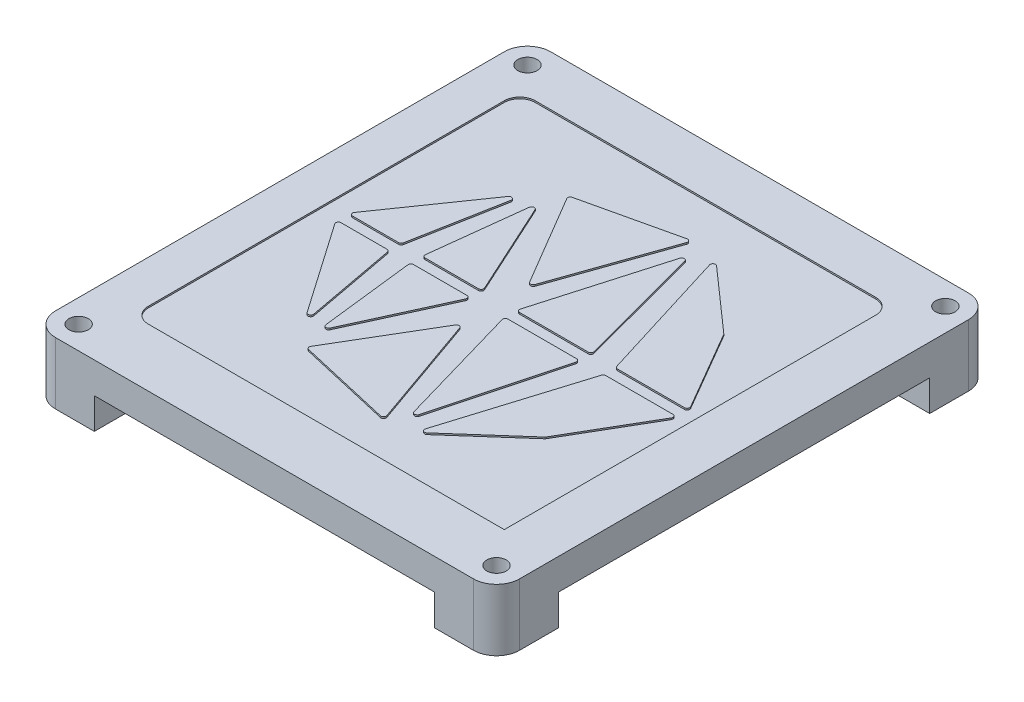
SolidWorks part; units mm, degrees
ref_plane "前视基准面" through (0, 0, 0) normal (0, 0, 1) x (1, 0, 0)
ref_plane "上视基准面" through (0, 0, 0) normal (0, 1, 0) x (1, 0, 0)
ref_plane "右视基准面" through (0, 0, 0) normal (1, 0, 0) x (0, 0, -1)
other "Configuration Table"
sketch "草图1" plane through (0, 0, 0) normal (0, 1, 0) x (1, 0, 0)
  line L8 (-27.0001, -31.9874) -> (27.0001, -31.9874)
  line L9 (29.9874, -29.0001) -> (29.9874, 29.0001)
  line L10 (27.0001, 31.9874) -> (-27.0001, 31.9874)
  line L11 (-29.9874, 29.0001) -> (-29.9874, -29.0001)
  line L12 (-27.0001, -31.9874) -> (27.0001, -31.9874)
  line L13 (29.9874, -29.0001) -> (29.9874, 29.0001)
  line L14 (27.0001, 31.9874) -> (-27.0001, 31.9874)
  line L15 (-29.9874, 29.0001) -> (-29.9874, -29.0001)
  arc A4 (27.0001, -31.9874) -> (29.9874, -29.0001) centre (27.0001, -29.0001) ccw
  arc A5 (29.9874, 29.0001) -> (27.0001, 31.9874) centre (27.0001, 29.0001) ccw
  arc A6 (-27.0001, 31.9874) -> (-29.9874, 29.0001) centre (-27.0001, 29.0001) ccw
  arc A7 (-29.9874, -29.0001) -> (-27.0001, -31.9874) centre (-27.0001, -29.0001) ccw
  arc A8 (27.0001, -31.9874) -> (29.9874, -29.0001) centre (27.0001, -29.0001) ccw
  arc A9 (29.9874, 29.0001) -> (27.0001, 31.9874) centre (27.0001, 29.0001) ccw
  arc A10 (-27.0001, 31.9874) -> (-29.9874, 29.0001) centre (-27.0001, 29.0001) ccw
  arc A11 (-29.9874, -29.0001) -> (-27.0001, -31.9874) centre (-27.0001, -29.0001) ccw
  dimension "D1" = 0
extrude "凸台-拉伸1" add sketch "草图1" along normal blind 4
sketch "草图2" plane through (0, 0, 0) normal (0, -1, 0) x (1, 0, 0)
  line L4 (-21.9874, 23.9874) -> (-21.9874, 31.9874)
  line L5 (-21.9874, 31.9874) -> (-27.0001, 31.9874)
  line L6 (-29.9874, 29.0001) -> (-29.9874, 23.9874)
  line L7 (-29.9874, 23.9874) -> (-21.9874, 23.9874)
  line L8 (-21.9874, 23.9874) -> (-21.9874, 31.9874)
  line L9 (-21.9874, 31.9874) -> (-27.0001, 31.9874)
  line L10 (-29.9874, 29.0001) -> (-29.9874, 23.9874)
  line L11 (-29.9874, 23.9874) -> (-21.9874, 23.9874)
  line L12 (21.9874, -23.9874) -> (21.9874, -31.9874)
  line L13 (21.9874, -31.9874) -> (27.0001, -31.9874)
  line L14 (29.9874, -29.0001) -> (29.9874, -23.9874)
  line L15 (29.9874, -23.9874) -> (21.9874, -23.9874)
  line L16 (21.9874, -23.9874) -> (21.9874, -31.9874)
  line L17 (21.9874, -31.9874) -> (27.0001, -31.9874)
  line L18 (29.9874, -29.0001) -> (29.9874, -23.9874)
  line L19 (29.9874, -23.9874) -> (21.9874, -23.9874)
  line L20 (21.9874, 23.9874) -> (29.9874, 23.9874)
  line L21 (29.9874, 23.9874) -> (29.9874, 29.0001)
  line L22 (27.0001, 31.9874) -> (21.9874, 31.9874)
  line L23 (21.9874, 31.9874) -> (21.9874, 23.9874)
  line L24 (21.9874, 23.9874) -> (29.9874, 23.9874)
  line L25 (29.9874, 23.9874) -> (29.9874, 29.0001)
  line L26 (27.0001, 31.9874) -> (21.9874, 31.9874)
  line L27 (21.9874, 31.9874) -> (21.9874, 23.9874)
  line L28 (-29.9874, -23.9874) -> (-29.9874, -29.0001)
  line L29 (-21.9874, -23.9874) -> (-29.9874, -23.9874)
  line L30 (-21.9874, -31.9874) -> (-21.9874, -23.9874)
  line L31 (-27.0001, -31.9874) -> (-21.9874, -31.9874)
  line L32 (-29.9874, -23.9874) -> (-29.9874, -29.0001)
  line L33 (-21.9874, -23.9874) -> (-29.9874, -23.9874)
  line L34 (-21.9874, -31.9874) -> (-21.9874, -23.9874)
  line L35 (-27.0001, -31.9874) -> (-21.9874, -31.9874)
  arc A1 (-27.0001, 31.9874) -> (-29.9874, 29.0001) centre (-27.0001, 29.0001) ccw
  arc A2 (-27.0001, 31.9874) -> (-29.9874, 29.0001) centre (-27.0001, 29.0001) ccw
  arc A3 (27.0001, -31.9874) -> (29.9874, -29.0001) centre (27.0001, -29.0001) ccw
  arc A4 (27.0001, -31.9874) -> (29.9874, -29.0001) centre (27.0001, -29.0001) ccw
  arc A5 (29.9874, 29.0001) -> (27.0001, 31.9874) centre (27.0001, 29.0001) ccw
  arc A6 (29.9874, 29.0001) -> (27.0001, 31.9874) centre (27.0001, 29.0001) ccw
  arc A7 (-29.9874, -29.0001) -> (-27.0001, -31.9874) centre (-27.0001, -29.0001) ccw
  arc A8 (-29.9874, -29.0001) -> (-27.0001, -31.9874) centre (-27.0001, -29.0001) ccw
  dimension "D1" = 0
  dimension "D2" = 0
  dimension "D3" = 0
  dimension "D4" = 0
extrude "凸台-拉伸2" add sketch "草图2" along normal blind 4
sketch "草图3" plane through (0, -4, 0) normal (0, -1, 0) x (1, 0, 0)
  circle A0 centre (-27.0001, 29.0001) radius 1.25
  circle A1 centre (27.0001, 29.0001) radius 1.25
  circle A2 centre (27.0001, -29.0001) radius 1.25
  circle A3 centre (-27.0001, -29.0001) radius 1.25
  dimension "D1" = 2.5
  dimension "D2" = 2.5
  dimension "D3" = 2.5
  dimension "D4" = 2.5
extrude "切除-拉伸1" cut sketch "草图3" against normal blind 15
sketch "草图5" plane through (0, 4, 0) normal (0, 1, 0) x (1, 0, 0)
  line L62 (-15.4572, -0.6885) -> (-21.4047, -0.6885)
  line L63 (-21.6811, -1.2171) -> (-13.5463, -12.9327)
  line L64 (-12.9389, -12.679) -> (-15.1263, -0.9633)
  line L65 (-13.5463, 13.0483) -> (-21.6811, 1.3327)
  line L66 (-21.4047, 0.8041) -> (-15.4572, 0.8041)
  line L67 (-15.1263, 1.0789) -> (-12.9389, 12.7946)
  line L68 (-10.9698, 13.2091) -> (-12.3754, 1.1798)
  line L69 (-12.0411, 0.8041) -> (-5.1311, 0.8041)
  line L70 (-4.825, 1.2808) -> (-10.3294, 13.3101)
  line L71 (-5.1311, -0.6885) -> (-12.0411, -0.6885)
  line L72 (-12.3754, -1.0642) -> (-10.9698, -13.0935)
  line L73 (-10.3294, -13.1945) -> (-4.825, -1.1652)
  line L74 (-2.5713, -4.7347) -> (-9.5126, -16.4728)
  line L75 (-9.2984, -16.9722) -> (2.7471, -19.7455)
  line L76 (3.1402, -19.3058) -> (-1.964, -4.7943)
  line L77 (5.1091, -17.1135) -> (9.3621, -1.1116)
  line L78 (9.0368, -0.6885) -> (0.1709, -0.6885)
  line L79 (-0.1525, -1.1183) -> (4.4604, -17.1202)
  line L80 (21.4842, -0.6885) -> (12.8085, -0.6885)
  line L81 (12.4869, -0.9258) -> (7.1237, -18.2969)
  line L82 (7.6683, -18.6483) -> (15.7557, -11.4981)
  line L83 (15.8237, -11.4153) -> (21.7751, -1.1945)
  line L84 (12.8085, 0.8041) -> (21.4842, 0.8041)
  line L85 (21.7751, 1.3101) -> (15.8237, 11.5309)
  line L86 (15.7557, 11.6137) -> (7.6683, 18.7639)
  line L87 (7.1237, 18.4125) -> (12.4869, 1.0414)
  line L88 (0.1709, 0.8041) -> (9.0368, 0.8041)
  line L89 (9.3621, 1.2272) -> (5.1091, 17.2291)
  line L90 (4.4604, 17.2358) -> (-0.1525, 1.2339)
  line L91 (-9.5126, 16.5885) -> (-2.5713, 4.8503)
  line L92 (-1.964, 4.91) -> (3.1402, 19.4214)
  line L93 (2.7471, 19.8611) -> (-9.2984, 17.0878)
  line L95 (-22.5102, -24.4894) -> (23.4898, -24.4894)
  line L96 (-24.5102, -22.4894) -> (-24.5102, 23.5106)
  line L97 (-22.5102, 25.5106) -> (21.4898, 25.5106)
  line L98 (23.4898, -24.4894) -> (23.4898, 23.5106)
  line L99 (-0.5102, 25.5106) -> (0.4898, -24.4894) construction
  line L100 (-24.5102, 0.5106) -> (23.4898, -0.4894) construction
  arc A48 (-15.1263, -0.9633) -> (-15.4572, -0.6885) centre (-15.4572, -1.0251) ccw
  arc A49 (-21.4047, -0.6885) -> (-21.6811, -1.2171) centre (-21.4047, -1.0251) ccw
  arc A50 (-13.5463, -12.9327) -> (-13.2698, -13.0773) centre (-13.2698, -12.7407) ccw
  arc A51 (-13.2698, -13.0773) -> (-12.9389, -12.679) centre (-13.2698, -12.7407) ccw
  arc A52 (-12.9389, 12.7946) -> (-13.5463, 13.0483) centre (-13.2698, 12.8564) ccw
  arc A53 (-21.6811, 1.3327) -> (-21.4047, 0.8041) centre (-21.4047, 1.1407) ccw
  arc A54 (-15.4572, 0.8041) -> (-15.1263, 1.0789) centre (-15.4572, 1.1407) ccw
  arc A55 (-10.3294, 13.3101) -> (-10.9698, 13.2091) centre (-10.6355, 13.1701) ccw
  arc A56 (-12.3754, 1.1798) -> (-12.0411, 0.8041) centre (-12.0411, 1.1407) ccw
  arc A57 (-5.1311, 0.8041) -> (-4.825, 1.2808) centre (-5.1311, 1.1407) ccw
  arc A58 (-4.825, -1.1652) -> (-5.1311, -0.6885) centre (-5.1311, -1.0251) ccw
  arc A59 (-12.0411, -0.6885) -> (-12.3754, -1.0642) centre (-12.0411, -1.0251) ccw
  arc A60 (-10.9698, -13.0935) -> (-10.6355, -13.391) centre (-10.6355, -13.0544) ccw
  arc A61 (-10.6355, -13.391) -> (-10.3294, -13.1945) centre (-10.6355, -13.0544) ccw
  arc A62 (-1.964, -4.7943) -> (-2.5713, -4.7347) centre (-2.2815, -4.906) ccw
  arc A63 (-9.5126, -16.4728) -> (-9.2984, -16.9722) centre (-9.2229, -16.6442) ccw
  arc A64 (2.7471, -19.7455) -> (2.8226, -19.7541) centre (2.8226, -19.4175) ccw
  arc A65 (2.8226, -19.7541) -> (3.1402, -19.3058) centre (2.8226, -19.4175) ccw
  arc A66 (4.4604, -17.1202) -> (4.7838, -17.3636) centre (4.7838, -17.027) ccw
  arc A67 (4.7838, -17.3636) -> (5.1091, -17.1135) centre (4.7838, -17.027) ccw
  arc A68 (9.3621, -1.1116) -> (9.0368, -0.6885) centre (9.0368, -1.0251) ccw
  arc A69 (0.1709, -0.6885) -> (-0.1525, -1.1183) centre (0.1709, -1.0251) ccw
  arc A70 (21.7751, -1.1945) -> (21.4842, -0.6885) centre (21.4842, -1.0251) ccw
  arc A71 (12.8085, -0.6885) -> (12.4869, -0.9258) centre (12.8085, -1.0251) ccw
  arc A72 (7.1237, -18.2969) -> (7.4453, -18.7328) centre (7.4453, -18.3962) ccw
  arc A73 (7.4453, -18.7328) -> (7.6683, -18.6483) centre (7.4453, -18.3962) ccw
  arc A74 (15.7557, -11.4981) -> (15.8237, -11.4153) centre (15.5328, -11.2459) ccw
  arc A75 (12.4869, 1.0414) -> (12.8085, 0.8041) centre (12.8085, 1.1407) ccw
  arc A76 (21.4842, 0.8041) -> (21.7751, 1.3101) centre (21.4842, 1.1407) ccw
  arc A77 (15.8237, 11.5309) -> (15.7557, 11.6137) centre (15.5328, 11.3615) ccw
  arc A78 (7.6683, 18.7639) -> (7.1237, 18.4125) centre (7.4453, 18.5118) ccw
  arc A79 (-0.1525, 1.2339) -> (0.1709, 0.8041) centre (0.1709, 1.1407) ccw
  arc A80 (9.0368, 0.8041) -> (9.3621, 1.2272) centre (9.0368, 1.1407) ccw
  arc A81 (5.1091, 17.2291) -> (4.4604, 17.2358) centre (4.7838, 17.1426) ccw
  arc A82 (-9.2984, 17.0878) -> (-9.5126, 16.5885) centre (-9.2229, 16.7598) ccw
  arc A83 (-2.5713, 4.8503) -> (-2.2815, 4.685) centre (-2.2815, 5.0216) ccw
  arc A84 (-2.2815, 4.685) -> (-1.964, 4.91) centre (-2.2815, 5.0216) ccw
  arc A85 (3.1402, 19.4214) -> (2.7471, 19.8611) centre (2.8226, 19.5331) ccw
  arc A86 (-24.5102, 23.5106) -> (-22.5102, 25.5106) centre (-22.5102, 23.5106) cw
  arc A87 (-22.5102, -24.4894) -> (-24.5102, -22.4894) centre (-22.5102, -22.4894) cw
  arc A88 (21.4898, 25.5106) -> (23.4898, 23.5106) centre (21.4898, 23.5106) cw
  point P102 (0, 0)
  point P108 (-24.5102, 25.5106)
  point P114 (-24.5102, -24.4894)
  dimension "D2" = 2
  dimension "D1" = 50
extrude "切除-拉伸2" cut sketch "草图5" against normal blind 0.2
